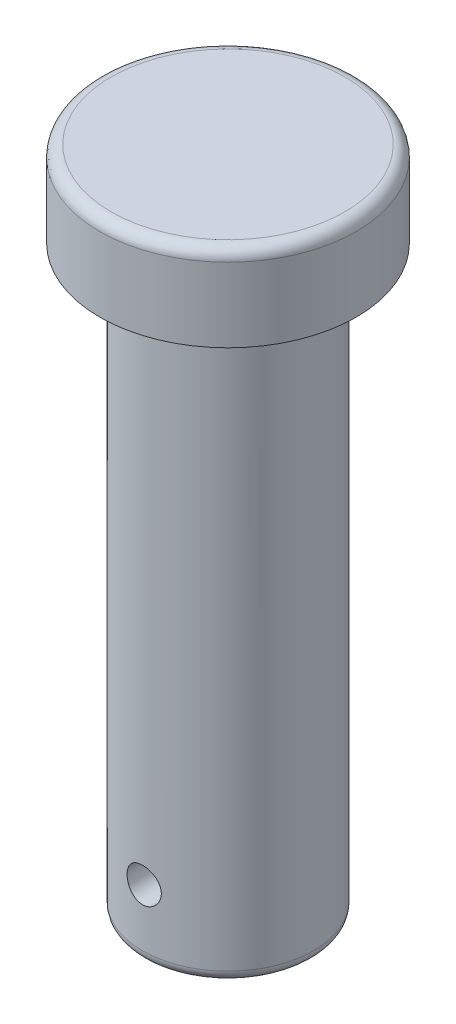
SolidWorks part; units mm, degrees
ref_plane "Front Plane" through (0, 0, 0) normal (0, 0, 1) x (1, 0, 0)
ref_plane "Top Plane" through (0, 0, 0) normal (0, 1, 0) x (1, 0, 0)
ref_plane "Right Plane" through (0, 0, 0) normal (1, 0, 0) x (0, 0, -1)
sketch "Sketch1" plane through (0, 0, 0) normal (0, 1, 0) x (1, 0, 0)
  circle A0 centre (0, 0) radius 22.5
  dimension "D1" = 45
extrude "Boss-Extrude1" add sketch "Sketch1" along normal blind 15
sketch "Sketch2" plane through (0, 0, 0) normal (0, -1, 0) x (1, 0, 0)
  circle A0 centre (0, 0) radius 15
  dimension "D1" = 30
extrude "Boss-Extrude2" add sketch "Sketch2" along normal blind 102
fillet "Fillet1" radius 2 3 edges at (0, -102, -15) (0, 15, 22.5) (0, 0, -15)
sketch "Sketch3" plane through (0, 0, 0) normal (0, 0, 1) x (1, 0, 0)
  line L0 (-13, -102) -> (13, -102) construction
  circle A0 centre (0, -90) radius 3
  point P4 (0, 0)
  dimension "D1" = 6
  dimension "D2" = 12
extrude "Cut-Extrude1" cut sketch "Sketch3" against normal through all both and the other way through all
